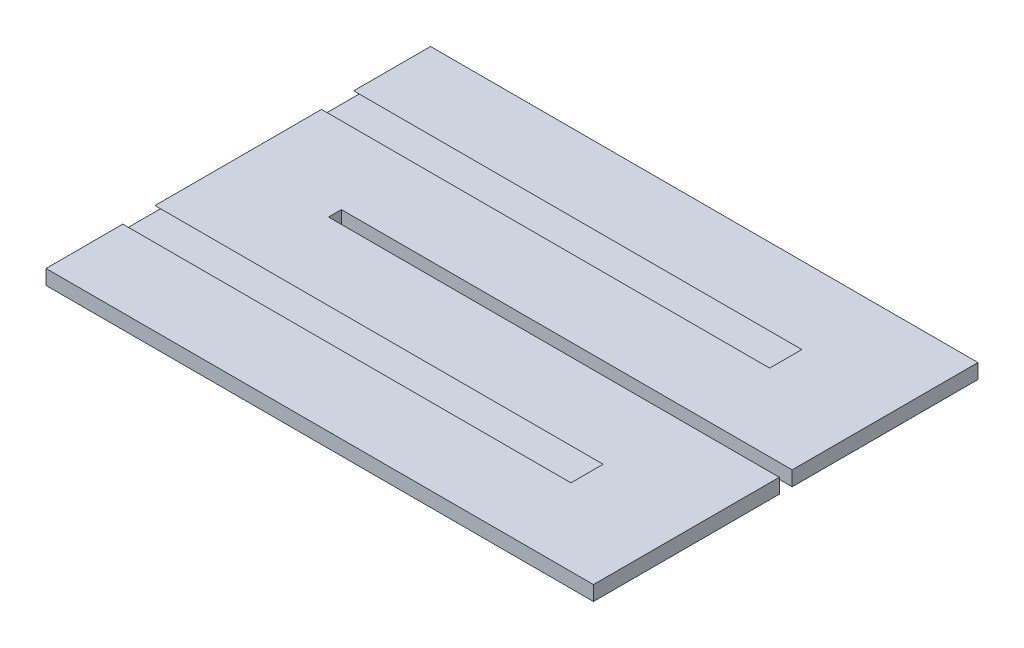
SolidWorks part; units mm, degrees
ref_plane "Front Plane" through (0, 0, 0) normal (0, 0, 1) x (1, 0, 0)
ref_plane "Top Plane" through (0, 0, 0) normal (0, 1, 0) x (1, 0, 0)
ref_plane "Right Plane" through (0, 0, 0) normal (1, 0, 0) x (0, 0, -1)
sketch "Sketch1" plane through (0, 0, 0) normal (0, 1, 0) x (1, 0, 0)
  line L0 (-13.4782, 10.45) -> (13.4782, 10.45)
  line L1 (-13.5782, -10.55) -> (13.5782, -10.55)
  line L2 (-13.5782, -10.55) -> (-13.5782, 10.55)
  line L3 (-13.5782, 10.55) -> (13.5782, 10.55)
  line L4 (13.5782, -10.55) -> (13.5782, 10.55)
  line L5 (-13.5782, -10.55) -> (13.5782, 10.55) construction
  line L6 (-13.5782, 10.55) -> (13.5782, -10.55) construction
  line L7 (13.4782, -10.45) -> (13.4782, 10.45)
  line L8 (-13.4782, -10.45) -> (13.4782, -10.45)
  line L9 (-13.4782, -10.45) -> (-13.4782, 10.45)
  line L10 (0, 0) -> (13.4782, 0) construction
  line L11 (13.4782, 0.35) -> (-8.2218, 0.35)
  line L12 (13.4782, -0.35) -> (-8.2218, -0.35)
  line L13 (-8.2218, -0.35) -> (-8.2218, 0.35)
  point P0 (0, 0)
  point P12 (13.4782, 0.35)
  dimension "D1" = 0.1
extrude "Boss-Extrude1" add sketch "Sketch1" along normal blind 0.8 contours L12 L13 L11 L7 L0 L9 L8
sketch "Sketch2" plane through (13.4782, 0, 0) normal (1, 0, 0) x (0, 0, -1)
  line L0 (-5.4, 0.8) -> (-5.4, 0) construction
  line L1 (-10.45, 0.8) -> (-0.35, 0.8) construction
  line L2 (-10.45, 0) -> (-0.35, 0) construction
  line L3 (-10.45, 0.4) -> (-0.35, 0.4) construction
  line L4 (-10.45, 0.8) -> (-10.45, 0) construction
  line L5 (-0.35, 0.8) -> (-0.35, 0) construction
  line L6 (-7.025, 0.5) -> (-3.775, 0.5)
  line L7 (-3.775, 0.5) -> (-4.525, 0.8)
  line L8 (-7.025, 0.5) -> (-6.275, 0.8)
  line L9 (-6.275, 0.8) -> (-4.525, 0.8)
  line L10 (-7.025, 0.3) -> (-6.275, 0)
  line L11 (-7.025, 0.3) -> (-3.775, 0.3)
  line L12 (-3.775, 0.3) -> (-4.525, 0)
  line L13 (-6.275, 0) -> (-4.525, 0)
  line L14 (0, 0) -> (0, 0.8) construction
  line L15 (7.025, 0.3) -> (3.775, 0.3)
  line L16 (3.775, 0.3) -> (4.525, 0)
  line L17 (6.275, 0) -> (4.525, 0)
  line L18 (7.025, 0.3) -> (6.275, 0)
  line L19 (7.025, 0.5) -> (6.275, 0.8)
  line L20 (7.025, 0.5) -> (3.775, 0.5)
  line L21 (3.775, 0.5) -> (4.525, 0.8)
  line L22 (6.275, 0.8) -> (4.525, 0.8)
  point P13 (-5.4, 0.5)
  point P14 (-5.4, 0.5)
  point P15 (-5.4, 0.5)
  point P16 (-5.4, 0.5)
  point P17 (-4.525, 0.8)
extrude "Cut-Extrude1" cut sketch "Sketch2" against normal blind 24.5 from offset 2.6 offset against normal yes
sketch "Sketch3" plane through (0, 0.8, 0) normal (0, 1, 0) x (1, 0, 0)
  line L0 (13.4782, -10.45) -> (-1.2, -10.45)
  line L1 (-13.4782, -10.45) -> (13.4782, -10.45) construction
  line L2 (-1.2, -10.45) -> (-1.2, 10.45)
  line L3 (-13.4782, 10.45) -> (13.4782, 10.45) construction
  line L4 (-1.2, 10.45) -> (13.4782, 10.45)
  line L5 (13.4782, 10.45) -> (13.4782, -10.45)
sketch "Sketch4" plane through (13.4782, 0, 0) normal (1, 0, 0) x (0, 0, -1)
  line L0 (-10.45, 0) -> (-10.45, 0.8)
  line L1 (-10.45, 0.8) -> (-0.35, 0.8)
  line L2 (-0.35, 0.8) -> (-0.35, 0)
  line L3 (-0.35, 0) -> (-10.45, 0)
  line L4 (0.35, 0) -> (0.35, 0.8)
  line L5 (0.35, 0.8) -> (10.45, 0.8)
  line L6 (10.45, 0.8) -> (10.45, 0)
  line L7 (10.45, 0) -> (0.35, 0)
extrude "Boss-Extrude2" add sketch "Sketch4" along normal blind 2.8
